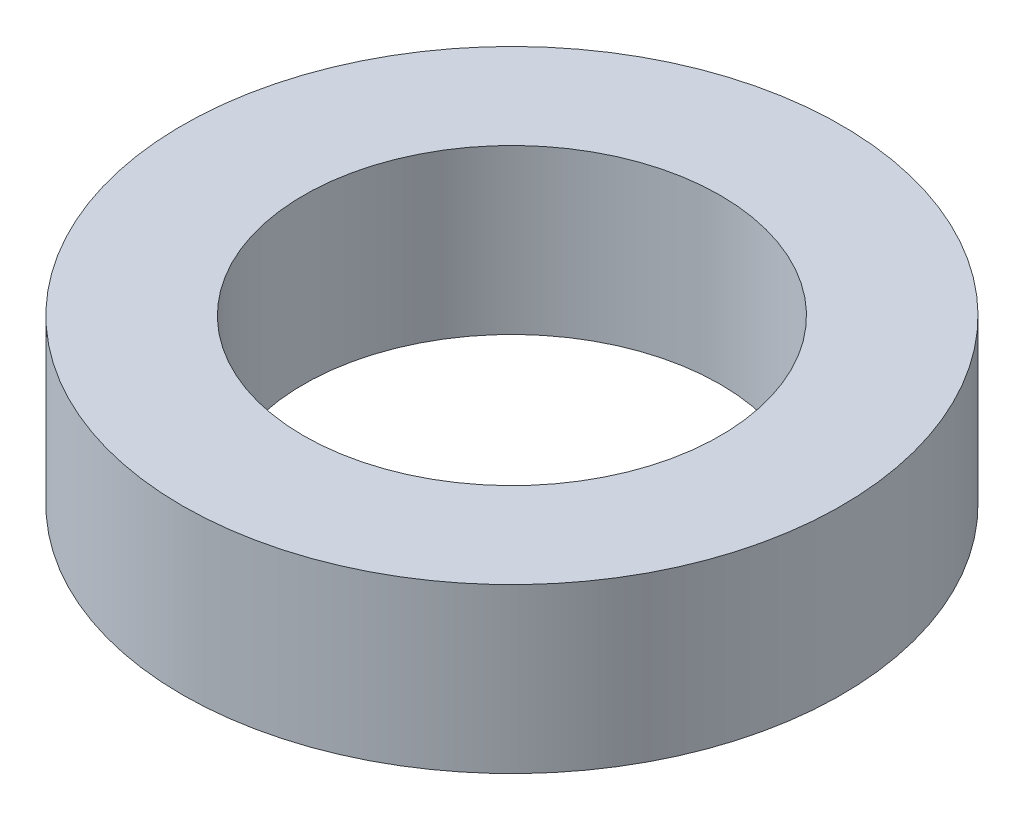
SolidWorks part; units mm, degrees
ref_plane "Front Plane" through (0, 0, 0) normal (0, 0, 1) x (1, 0, 0)
ref_plane "Top Plane" through (0, 0, 0) normal (0, 1, 0) x (1, 0, 0)
ref_plane "Right Plane" through (0, 0, 0) normal (1, 0, 0) x (0, 0, -1)
sketch "Sketch1" plane through (0, 0, 0) normal (0, 1, 0) x (1, 0, 0)
  circle A0 centre (0, 0) radius 11.075
  dimension "D1" = 22.15
extrude "Boss-Extrude1" add sketch "Sketch1" along normal blind 5.5
sketch "Sketch2" plane through (0, 5.5, 0) normal (0, 1, 0) x (1, 0, 0)
  circle A0 centre (0, 0) radius 7
  dimension "D1" = 14
extrude "Cut-Extrude1" cut sketch "Sketch2" against normal up to surface (5.5 mm away) up to face at (0, 0, 11.075)
